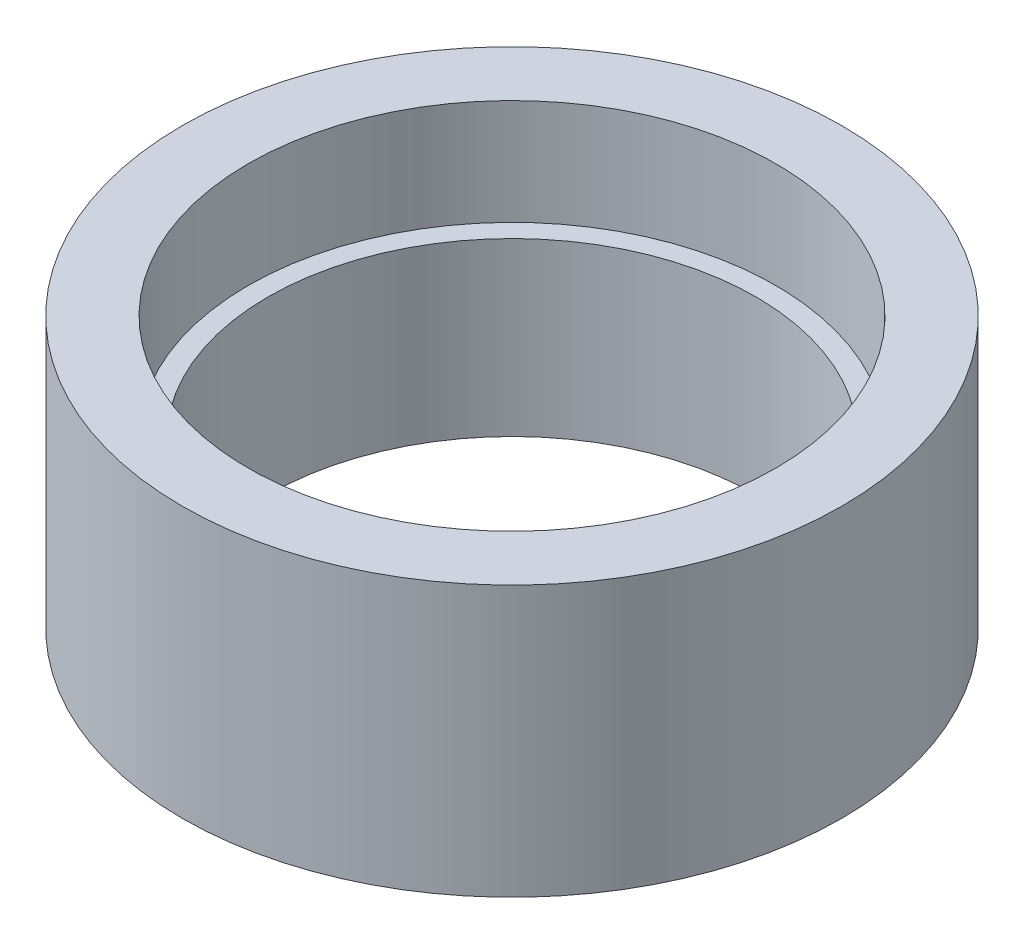
SolidWorks part; units mm, degrees
ref_plane "前基準面" through (0, 0, 0) normal (0, 0, 1) x (1, 0, 0)
ref_plane "上基準面" through (0, 0, 0) normal (0, 1, 0) x (1, 0, 0)
ref_plane "右基準面" through (0, 0, 0) normal (1, 0, 0) x (0, 0, -1)
sketch "草圖1" plane through (0, 0, 0) normal (0, 0, 1) x (1, 0, 0)
  line L0 (0, 36.4862) -> (0, -42) construction
  line L1 (40, 0) -> (50, 0)
  line L2 (50, 0) -> (50, -41)
  line L3 (50, -41) -> (40, -41)
  line L4 (40, -41) -> (40, -42)
  line L5 (40, -42) -> (37, -42)
  line L6 (37, -42) -> (37, -16)
  line L7 (37, -16) -> (40, -16)
  line L8 (40, -16) -> (40, 0)
  point P3 (0, 0)
  point P5 (0, 0)
  point P13 (0, -32.4608)
  point P14 (0, 0)
  point P15 (0, 0)
  dimension "D1" = 74
  dimension "D2" = 80
  dimension "D3" = 16
  dimension "D4" = 41
  dimension "D5" = 1
  dimension "D6" = 80
  dimension "D7" = 100
revolve "旋轉1" add sketch "草圖1" angle 360 about L0
